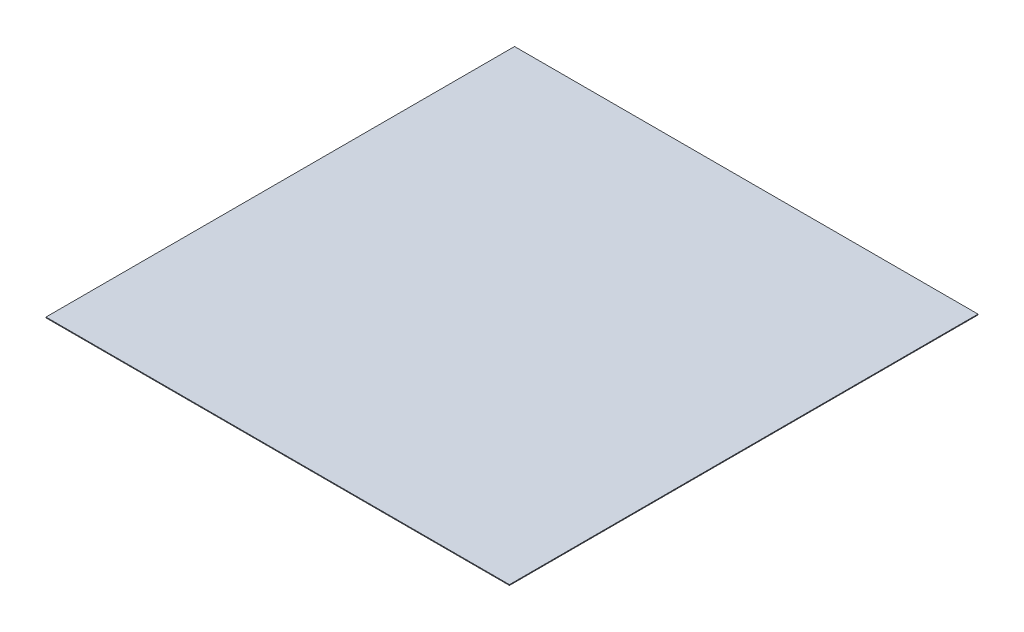
SolidWorks part; units mm, degrees
ref_plane "Front Plane" through (0, 0, 0) normal (0, 0, 1) x (1, 0, 0)
ref_plane "Top Plane" through (0, 0, 0) normal (0, 1, 0) x (1, 0, 0)
ref_plane "Right Plane" through (0, 0, 0) normal (1, 0, 0) x (0, 0, -1)
sketch "Sketch1" plane through (0, 0, 0) normal (0, 1, 0) x (1, 0, 0)
  line L1 (-455, -460) -> (455, -460)
  line L2 (-455, -460) -> (-455, 460)
  line L3 (-455, 460) -> (455, 460)
  line L4 (455, -460) -> (455, 460)
  line L5 (-455, -460) -> (455, 460) construction
  line L6 (-455, 460) -> (455, -460) construction
  point P0 (0, 0)
  dimension "D1" = 910
  dimension "D2" = 920
extrude "Boss-Extrude1" add sketch "Sketch1" along normal blind 1.5
